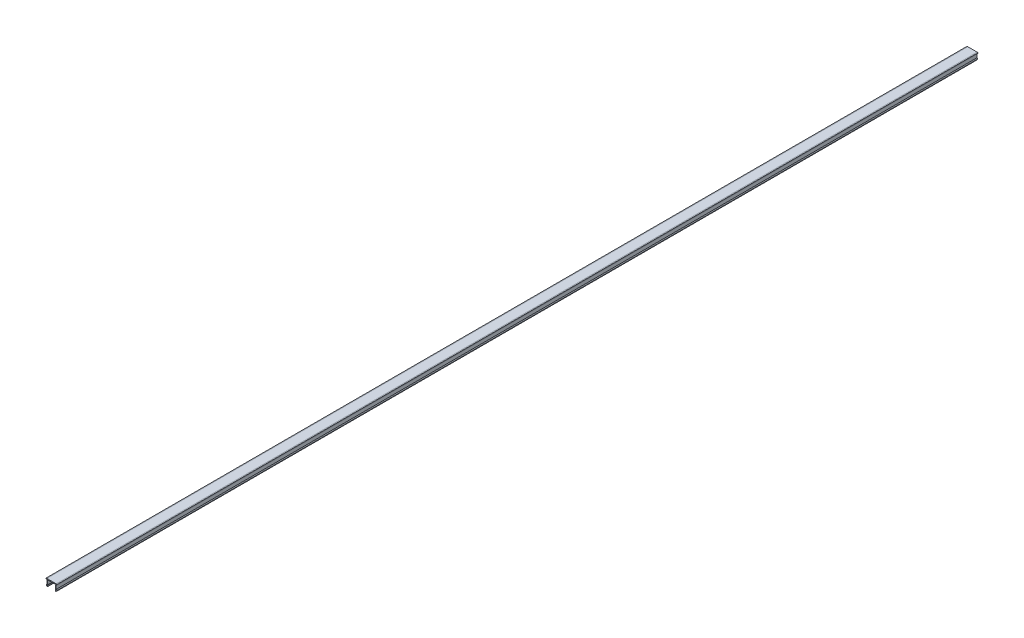
SolidWorks part; units mm, degrees
material "Пластик"
ref_plane "Спереди" through (0, 0, 0) normal (0, 0, 1) x (1, 0, 0)
ref_plane "Сверху" through (0, 0, 0) normal (0, 1, 0) x (1, 0, 0)
ref_plane "Справа" through (0, 0, 0) normal (1, 0, 0) x (0, 0, -1)
sketch "Эскиз1" plane through (0, 0, 0) normal (0, 0, 1) x (1, 0, 0)
  line L21 (-5.1, 0) -> (-6, -0.1587)
  line L22 (-6, -0.1587) -> (-6, -0.8)
  line L23 (-6, -0.8) -> (-5.1, -0.8)
  line L24 (-5.1, -0.8) -> (-5.1, -5.1962)
  line L25 (-5.1, -5.1962) -> (-5.6877, -6.2141)
  line L26 (-5.6877, -6.2141) -> (-5.1, -7.2321)
  line L27 (-4.1, -6.9641) -> (-4.533, -6.2141)
  line L28 (-4.533, -6.2141) -> (-4.1, -5.4641)
  line L29 (-4.1, -5.4641) -> (-4.1, -1)
  line L30 (-4.1, -1) -> (4.1, -1)
  line L31 (-5.1, 0) -> (5.1, 0)
  line L32 (0, 0) -> (0, -1) construction
  line L33 (4.1, -5.4641) -> (4.1, -1)
  line L34 (4.533, -6.2141) -> (4.1, -5.4641)
  line L35 (4.1, -6.9641) -> (4.533, -6.2141)
  line L36 (5.6877, -6.2141) -> (5.1, -7.2321)
  line L37 (5.1, -5.1962) -> (5.6877, -6.2141)
  line L38 (5.1, -0.8) -> (5.1, -5.1962)
  line L39 (6, -0.8) -> (5.1, -0.8)
  line L40 (6, -0.1587) -> (6, -0.8)
  line L41 (5.1, 0) -> (6, -0.1587)
  arc A0 (-5.1, -7.2321) -> (-4.1, -6.9641) centre (-4.6359, -6.9641) ccw
  arc A1 (5.1, -7.2321) -> (4.1, -6.9641) centre (4.6359, -6.9641) cw
  point P2 (-2.361, -1.7969)
  point P28 (-2.5404, 0)
  point P29 (-2.1, -5.8959)
  point P30 (-1.9938, -7.2818)
  point P31 (-3.6877, -6.0654)
  point P32 (-2.1, -6.985)
  dimension "D1" = 12
  dimension "D2" = 10.2
  dimension "D3" = 7.5
  dimension "D4" = 150
  dimension "D5" = 120
  dimension "D6" = 1
  dimension "D7" = 1
  dimension "D8" = 1
  dimension "D9" = 0.8
  dimension "D10" = 1
  dimension "D11" = 10
  dimension "D12" = 1.5
extrude "Бобышка-Вытянуть1" add sketch "Эскиз1" along normal blind 1000
